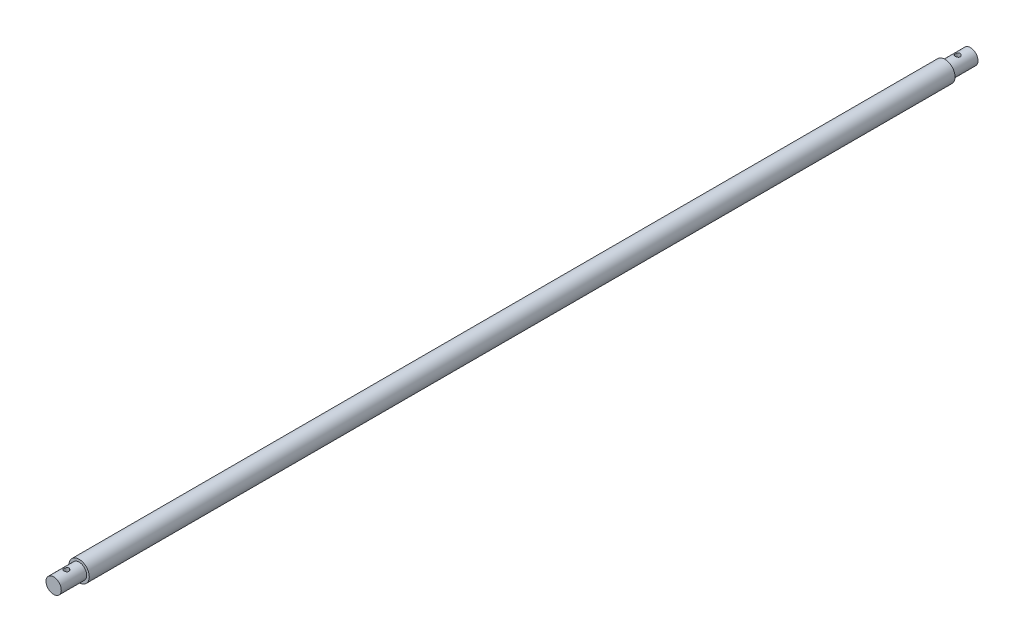
SolidWorks part; units mm, degrees
material "Plain Carbon Steel"
ref_plane "Front Plane" through (0, 0, 0) normal (0, 0, 1) x (1, 0, 0)
ref_plane "Top Plane" through (0, 0, 0) normal (0, 1, 0) x (1, 0, 0)
ref_plane "Right Plane" through (0, 0, 0) normal (1, 0, 0) x (0, 0, -1)
sketch "Sketch1" plane through (0, 0, 0) normal (0, 0, 1) x (1, 0, 0)
  circle A0 centre (0, 0) radius 4
  dimension "D1" = 8
extrude "Boss-Extrude1" add sketch "Sketch1" along normal blind 350
sketch "Sketch2" plane through (0, 0, 350) normal (0, 0, 1) x (1, 0, 0)
  circle A0 centre (0, 0) radius 3
extrude "Boss-Extrude2" add sketch "Sketch2" along normal blind 10
sketch "Sketch3" plane through (0, 0, 0) normal (0, 1, 0) x (1, 0, 0)
  line L0 (-3, -360) -> (3, -360) construction
  line L1 (-3, -350) -> (-3, -360) construction
  circle A0 centre (0, -355) radius 1
  dimension "D1" = 2
  dimension "D2" = 5
  dimension "D3" = 3
extrude "Cut-Extrude1" cut sketch "Sketch3" along normal mid plane 6
sketch "Sketch5" plane through (0, 0, 0) normal (0, 0, -1) x (-1, 0, 0)
  circle A0 centre (0, 0) radius 4
  circle A1 centre (0, 0) radius 3
  dimension "D1" = 6
  dimension "D2" = 8
extrude "Cut-Extrude3" cut sketch "Sketch5" against normal blind 10
sketch "Sketch6" plane through (0, 0, 0) normal (0, 1, 0) x (1, 0, 0)
  line L0 (3, 0) -> (-3, 0) construction
  circle A0 centre (0, -5) radius 1
  dimension "D1" = 2
  dimension "D2" = 5
extrude "Cut-Extrude4" cut sketch "Sketch6" against normal through all and the other way through all
